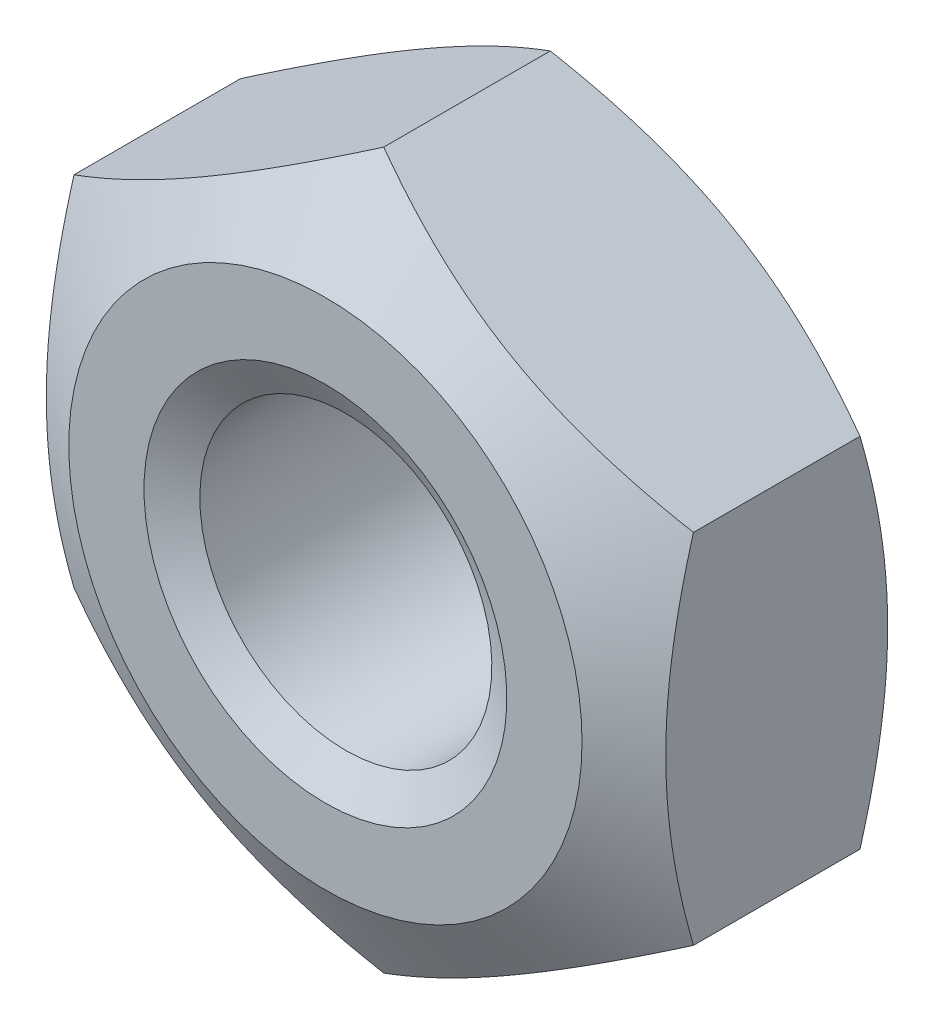
SolidWorks part; units mm, degrees
ref_plane "Front Plane" through (0, 0, 0) normal (0, 0, 1) x (1, 0, 0)
ref_plane "Top Plane" through (0, 0, 0) normal (0, 1, 0) x (1, 0, 0)
ref_plane "Right Plane" through (0, 0, 0) normal (1, 0, 0) x (0, 0, -1)
sketch "Sketch1" plane through (0, 0, 0) normal (0, 0, 1) x (1, 0, 0)
  line L0 (0, 0) -> (0, 4.0415) construction
  line L1 (0, 4.0415) -> (-3.5, 2.0207)
  line L2 (-3.5, 2.0207) -> (-3.5, -2.0207)
  line L3 (-3.5, -2.0207) -> (0, -4.0415)
  line L4 (0, -4.0415) -> (3.5, -2.0207)
  line L5 (3.5, -2.0207) -> (3.5, 2.0207)
  line L6 (3.5, 2.0207) -> (0, 4.0415)
  circle A0 centre (0, 0) radius 3.5 construction
  dimension "S DIM" = 7
extrude "Boss-Extrude1" add sketch "Sketch1" against normal blind 3.2
sketch "Sketch4" plane through (0, 0, 0) normal (1, 0, 0) x (0, 0, -1)
  line L0 (3.2, 4.0415) -> (2.541, 4.0415)
  line L1 (3.2, 4.0415) -> (0, 4.0415) construction
  line L2 (2.541, 4.0415) -> (3.2, 2.9)
  line L4 (3.2, 2.9) -> (3.2, 4.0415)
  line L5 (0, 0) -> (3.2979, 0) construction
  line L6 (0, 4.0415) -> (0.659, 4.0415)
  line L7 (0.659, 4.0415) -> (0, 2.9)
  line L9 (0, 2.9) -> (0, 4.0415)
  dimension "SAME S 1" = 5.8
  dimension "D2" = 30
  dimension "SAME S 2" = 5.8
  dimension "D4" = 30
revolve "Cut-Revolve1" cut sketch "Sketch4" angle 360 about L5
sketch "Sketch5" plane through (0, 0, 0) normal (1, 0, 0) x (0, 0, -1)
  line L0 (0, 0) -> (3.2, 0) construction
  line L1 (0, 0) -> (0, 2.05)
  line L2 (0, 2.9) -> (0, -2.9) construction
  line L3 (0, 2.05) -> (0.2309, 1.65)
  line L4 (0.2309, 1.65) -> (2.9691, 1.65)
  line L5 (2.9691, 1.65) -> (3.2, 2.05)
  line L6 (3.2, 2.05) -> (3.2, 0)
  line L8 (3.2, -2.9) -> (3.2, 2.9) construction
  line L9 (3.2, 0) -> (0, 0)
  dimension "D1" = 60
  dimension "D2" = 60
  dimension "Hole2" = 4.1
  dimension "Hole1" = 3.3
revolve "Cut-Revolve2" cut sketch "Sketch5" angle 360 about L0
cosmetic thread "Cosmetic Thread1" parameters "D2"=4
